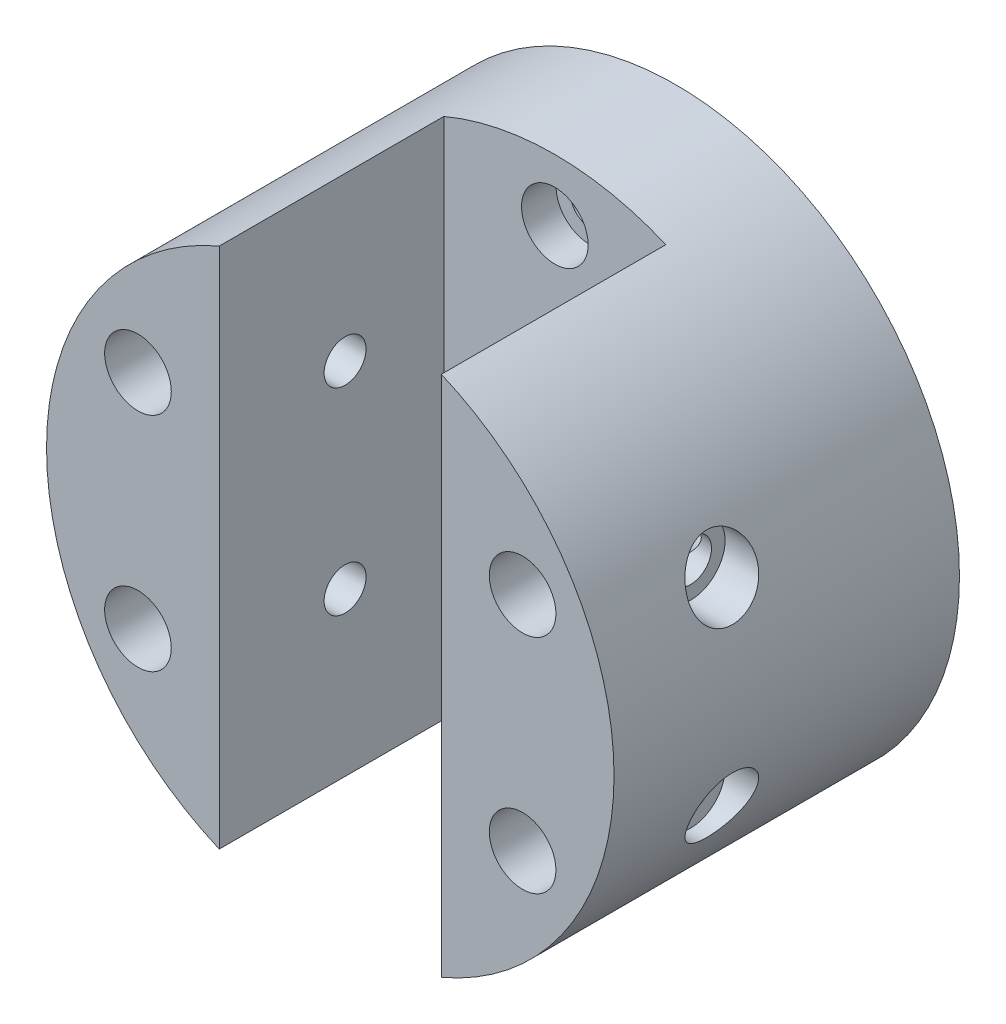
SolidWorks part; units mm, degrees
ref_plane "前视基准面" through (0, 0, 0) normal (0, 0, 1) x (1, 0, 0)
ref_plane "上视基准面" through (0, 0, 0) normal (0, 1, 0) x (1, 0, 0)
ref_plane "右视基准面" through (0, 0, 0) normal (1, 0, 0) x (0, 0, -1)
other "Configuration Table"
sketch "草图1" plane through (0, 0, 0) normal (0, 0, 1) x (1, 0, 0)
  circle A0 centre (0, 0) radius 23
extrude "凸台-拉伸1" add sketch "草图1" along normal blind 28
sketch "草图2" plane through (0, 0, 28) normal (0, 0, 1) x (1, 0, 0)
  line L0 (0, 0) -> (9, 0) construction
  line L1 (0, 0) -> (-9, 0) construction
  line L2 (-9, 21.166) -> (-9, -21.166)
  line L3 (9, 21.166) -> (9, -21.166)
  circle A0 centre (0, 0) radius 23 construction
  circle A1 centre (0, 0) radius 23
  circle M4 centre (0, 0) radius 23
extrude "切除-拉伸1" cut sketch "草图2" against normal blind 18.2 contours L3 L2 M4
sketch "草图3" plane through (0, 0, 28) normal (0, 0, 1) x (1, 0, 0)
  line L0 (0, 0) -> (0, 18) construction
  circle A0 centre (0, 18) radius 1.5
  circle A1 centre (15.5885, 9) radius 1.5
  circle A2 centre (15.5885, -9) radius 1.5
  circle A3 centre (0, -18) radius 1.5
  circle A4 centre (-15.5885, -9) radius 1.5
  circle A5 centre (-15.5885, 9) radius 1.5
  point P16 (0, 0)
  dimension "D1" = 6
extrude "切除-拉伸2" cut sketch "草图3" against normal through all
sketch "草图5" plane through (0, 0, 28) normal (0, 0, 1) x (1, 0, 0)
  circle A0 centre (0, 18) radius 2.7
  circle A1 centre (15.5885, 9) radius 2.7
  circle A2 centre (15.5885, -9) radius 2.7
  circle A3 centre (0, -18) radius 2.7
  circle A4 centre (-15.5885, -9) radius 2.7
  circle A5 centre (-15.5885, 9) radius 2.7
  point P15 (0, 0)
  dimension "D1" = 6
extrude "切除-拉伸3" cut sketch "草图5" against normal blind 21
sketch "草图7" plane through (9, 0, 0) normal (-1, 0, 0) x (0, 0, 1)
  line L0 (0, 0) -> (9.8, 0) construction
  line L1 (9.8, 0) -> (17.8, 0) construction
  line L2 (17.8, -8) -> (17.8, 8) construction
  circle A0 centre (17.8, 8) radius 1.7
  circle A1 centre (17.8, -8) radius 1.7
  point P7 (17.8, 0)
extrude "切除-拉伸4" cut sketch "草图7" against normal through all both and the other way through all
ref_plane "基准面1" through (23, 0, 0) normal (-1, 0, 0) x (0, 0, 1)
sketch "草图8" plane through (23, 0, 0) normal (-1, 0, 0) x (0, 0, 1)
  circle A0 centre (17.8, 8) radius 2.8
  circle A1 centre (17.8, -8) radius 2.8
extrude "切除-拉伸5" cut sketch "草图8" along normal blind 4
